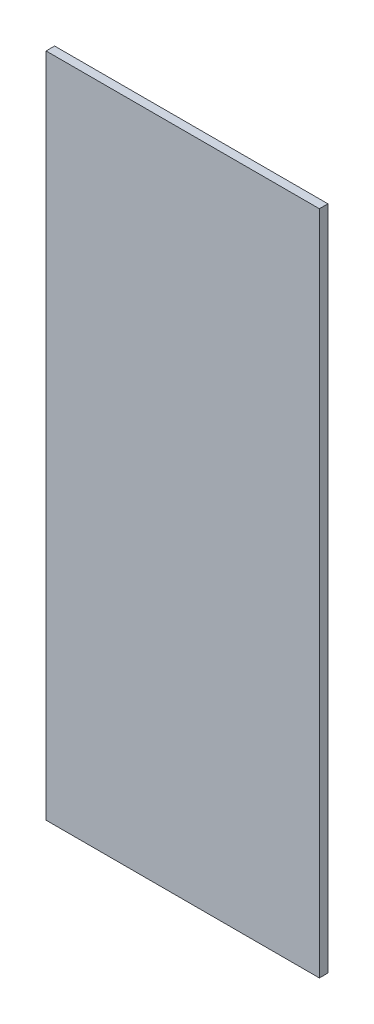
SolidWorks part; units mm, degrees
ref_plane "Alzado" through (0, 0, 0) normal (0, 0, 1) x (1, 0, 0)
ref_plane "Planta" through (0, 0, 0) normal (0, 1, 0) x (1, 0, 0)
ref_plane "Vista lateral" through (0, 0, 0) normal (1, 0, 0) x (0, 0, -1)
sketch "Croquis2" plane through (0, 0, 0) normal (0, 1, 0) x (1, 0, 0)
  line L1 (-101.6, 3.175) -> (101.6, 3.175)
  line L2 (-101.6, 3.175) -> (-101.6, -3.175)
  line L3 (-101.6, -3.175) -> (101.6, -3.175)
  line L4 (101.6, 3.175) -> (101.6, -3.175)
  line L5 (-101.6, 3.175) -> (101.6, -3.175) construction
  line L6 (-101.6, -3.175) -> (101.6, 3.175) construction
  point P0 (0, 0)
  dimension "D1" = 203.2
  dimension "D2" = 6.35
extrude "Saliente-Extruir1" add sketch "Croquis2" along normal blind 495.3
